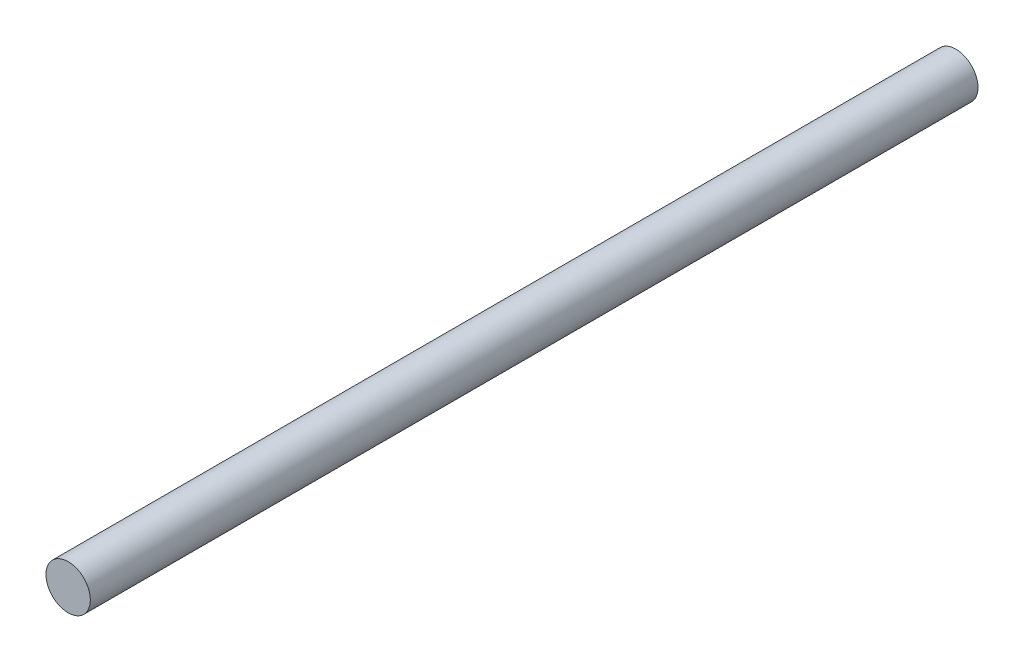
SolidWorks part; units mm, degrees
ref_plane "前视基准面" through (0, 0, 0) normal (0, 0, 1) x (1, 0, 0)
ref_plane "上视基准面" through (0, 0, 0) normal (0, 1, 0) x (1, 0, 0)
ref_plane "右视基准面" through (0, 0, 0) normal (1, 0, 0) x (0, 0, -1)
sketch "草图1" plane through (0, 0, 0) normal (0, 0, 1) x (1, 0, 0)
  circle A0 centre (0, 0) radius 7.5
  dimension "D1" = 15
extrude "凸台-拉伸1" add sketch "草图1" along normal blind 300
